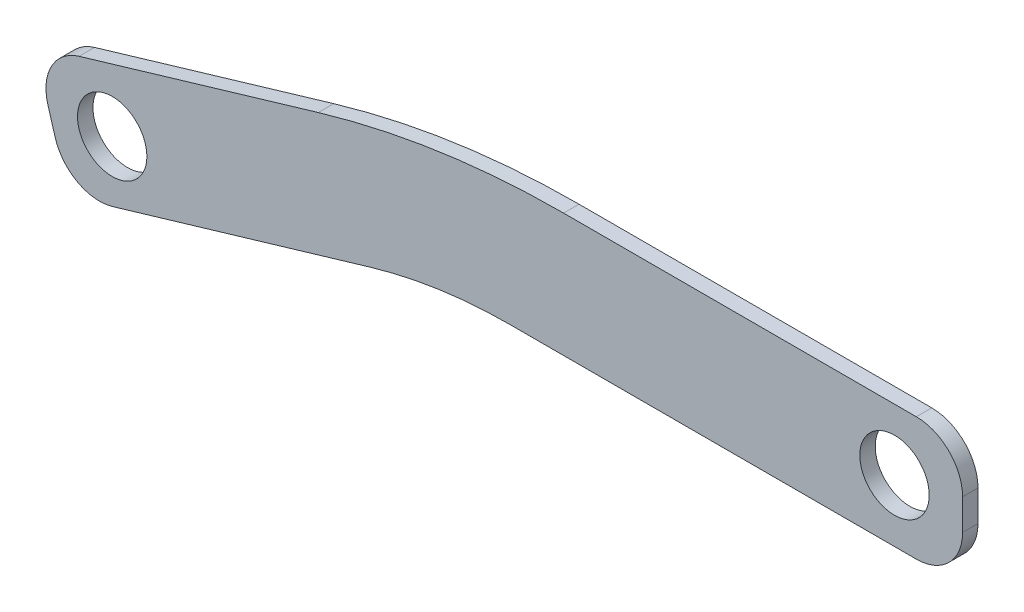
SolidWorks part; units mm, degrees
ref_plane "Front Plane" through (0, 0, 0) normal (0, 0, 1) x (1, 0, 0)
ref_plane "Top Plane" through (0, 0, 0) normal (0, 1, 0) x (1, 0, 0)
ref_plane "Right Plane" through (0, 0, 0) normal (1, 0, 0) x (0, 0, -1)
sketch "Sketch1" plane through (0, 0, 0) normal (0, 0, 1) x (1, 0, 0)
  line L0 (0, 0) -> (215.9, 0)
  line L1 (0, 0) -> (-152.4, -45.1556)
  line L2 (215.9, 0) -> (215.9, 50.8)
  line L3 (215.9, 50.8) -> (0, 50.8)
  line L4 (0, 50.8) -> (-166.2371, 1.5446)
  line L5 (-166.2371, 1.5446) -> (-152.4, -45.1556)
  point P3 (0, 50.8)
  dimension "D1" = 215.9
  dimension "D2" = 152.4
  dimension "D3" = 50.8
extrude "Boss-Extrude1" add sketch "Sketch1" along normal blind 6.35
fillet "Fillet1" radius 203.2 1 edges at (0, 0, 3.175)
fillet "Fillet2" radius 355.6 1 edges at (0, 50.8, 3.175)
fillet "Fillet3" radius 19.05 1 edges at (-166.2371, 1.5446, 3.175)
fillet "Fillet4" radius 19.05 1 edges at (-152.4, -45.1556, 3.175)
fillet "Fillet5" radius 19.05 1 edges at (215.9, 50.8, 3.175)
fillet "Fillet6" radius 19.05 1 edges at (215.9, 0, 3.175)
sketch "Sketch2" plane through (0, 0, 6.35) normal (0, 0, 1) x (1, 0, 0)
  circle A0 centre (-134.3302, -14.8254) radius 14.2875
  circle A1 centre (187.8589, 25.4485) radius 14.2875
  point P4 (-156.9151, -13.1772)
  point P5 (214.4461, 25.064)
  point P6 (-134.3302, -14.8254)
  point P7 (187.8589, 25.4485)
  dimension "D1" = 28.575
  dimension "D2" = 28.575
extrude "Cut-Extrude1" cut sketch "Sketch2" against normal blind 6.35
